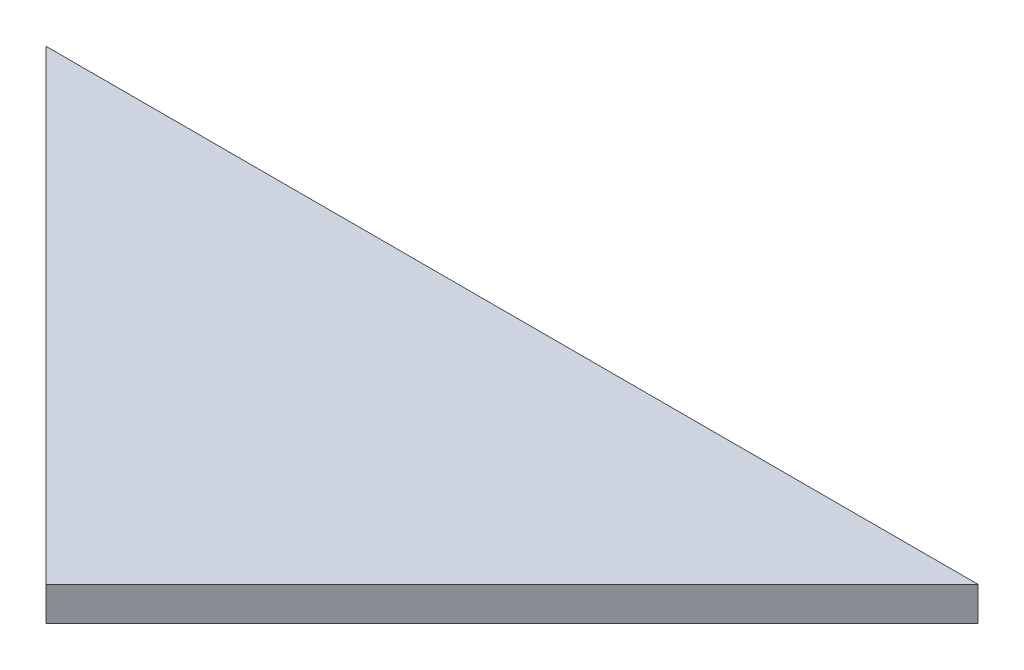
SolidWorks part; units mm, degrees
material "Acrylic (Medium-high impact)"
ref_plane "Front Plane" through (0, 0, 0) normal (0, 0, 1) x (1, 0, 0)
ref_plane "Top Plane" through (0, 0, 0) normal (0, 1, 0) x (1, 0, 0)
ref_plane "Right Plane" through (0, 0, 0) normal (1, 0, 0) x (0, 0, -1)
ref_plane "Plane1" through (0, -113.7049, 0) normal (0, -1, 0) x (-1, 0, 0)
sketch "Sketch1" plane through (0, -113.7049, 0) normal (0, -1, 0) x (-1, 0, 0)
  line L0 (40.966, -116.2449) -> (-40.966, -116.2449) construction
  line L1 (-40.966, -116.2449) -> (0, -157.2109) construction
  line L2 (0, -157.2109) -> (40.966, -116.2449) construction
  line L3 (40.966, -116.2449) -> (-40.966, -116.2449)
  line L4 (-40.966, -116.2449) -> (0, -157.2109)
  line L5 (0, -157.2109) -> (40.966, -116.2449)
extrude "Boss-Extrude1" add sketch "Sketch1" along normal mid plane 3
